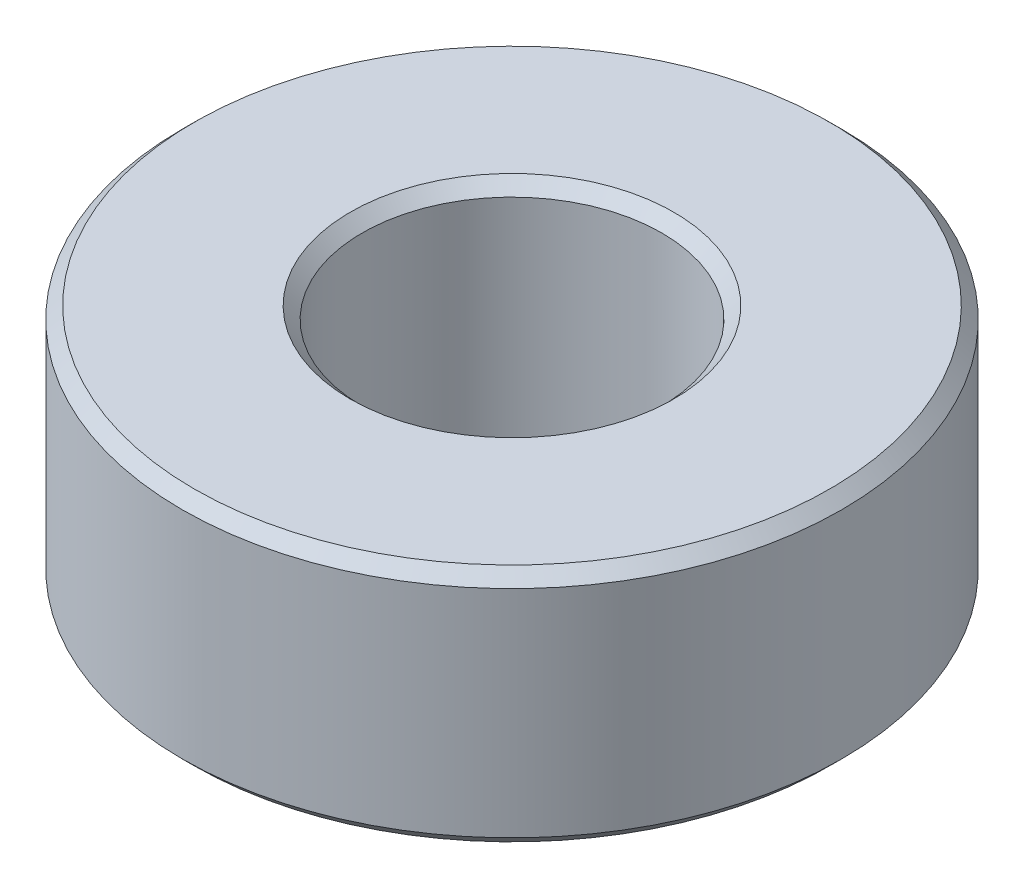
SolidWorks part; units mm, degrees
material "201 Annealed Stainless Steel (SS)"
ref_plane "Front Plane" through (0, 0, 0) normal (0, 0, 1) x (1, 0, 0)
ref_plane "Top Plane" through (0, 0, 0) normal (0, 1, 0) x (1, 0, 0)
ref_plane "Right Plane" through (0, 0, 0) normal (1, 0, 0) x (0, 0, -1)
sketch "Sketch1" plane through (0, 0, 0) normal (0, 1, 0) x (1, 0, 0)
  circle A0 centre (0, 0) radius 2.5
  circle A1 centre (0, 0) radius 5.5
  dimension "D1" = 11
  dimension "D2" = 5
extrude "Boss-Extrude1" add sketch "Sketch1" along normal blind 4
chamfer "Chamfer1" distance 0.2 angle 45 4 edges at (0, 4, 5.5) (0, 0, 2.5) (0, 4, 2.5) (0, 0, 5.5)
